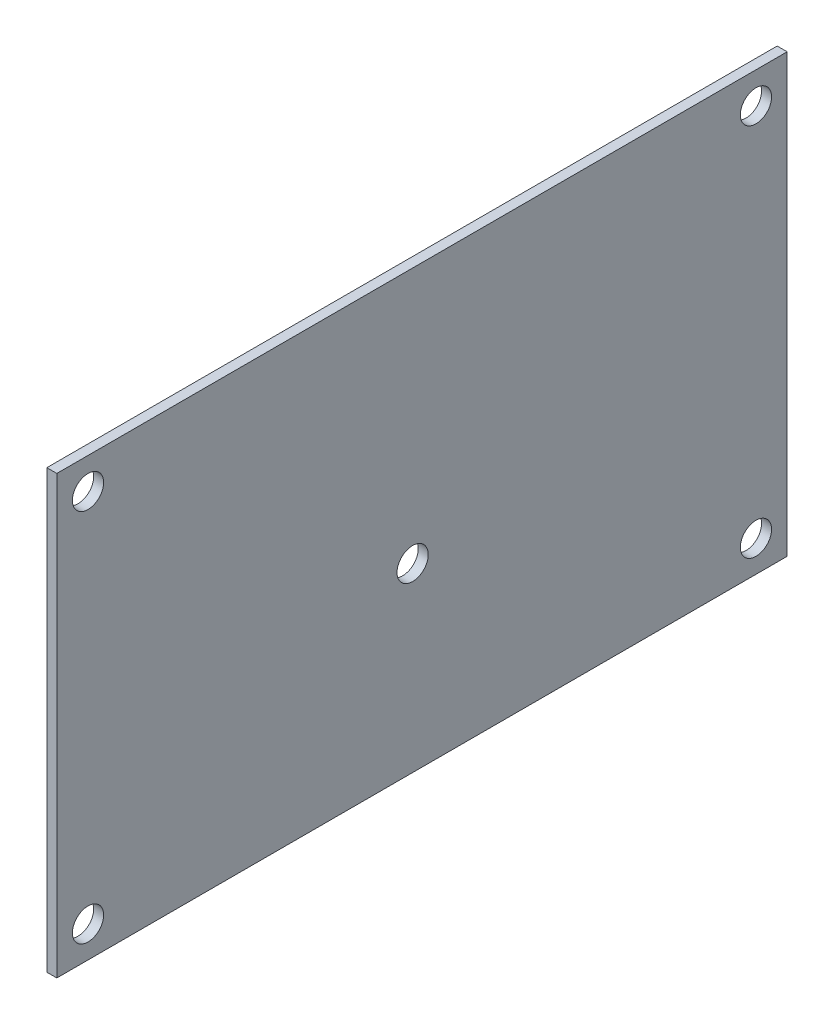
SolidWorks part; units mm, degrees
ref_plane "Front Plane" through (0, 0, 0) normal (0, 0, 1) x (1, 0, 0)
ref_plane "Top Plane" through (0, 0, 0) normal (0, 1, 0) x (1, 0, 0)
ref_plane "Right Plane" through (0, 0, 0) normal (1, 0, 0) x (0, 0, -1)
sketch "Sketch1" plane through (0, 0, 0) normal (1, 0, 0) x (0, 0, -1)
  line L1 (0, 0) -> (117, 0)
  line L2 (0, 0) -> (0, 70)
  line L3 (0, 70) -> (117, 70)
  line L4 (117, 0) -> (117, 70)
  dimension "D1" = 117
  dimension "D2" = 70
extrude "Boss-Extrude1" add sketch "Sketch1" along normal blind 1.6
sketch "Sketch2" plane through (1.6, 0, 0) normal (1, 0, 0) x (0, 0, -1)
  line L0 (117, 70) -> (0, 70) construction
  line L1 (0, 70) -> (0, 0) construction
  line L2 (0, 0) -> (117, 0) construction
  line L3 (117, 0) -> (117, 70) construction
  circle A0 centre (5, 65) radius 2.5
  circle A1 centre (5, 5) radius 2.5
  circle A2 centre (112, 5) radius 2.5
  circle A3 centre (112, 65) radius 2.5
  circle A4 centre (57, 29) radius 2.5
  dimension "D1" = 5
  dimension "D3" = 5
  dimension "D9" = 57
  dimension "D2" = 5
  dimension "D4" = 5
  dimension "D5" = 5
  dimension "D6" = 5
  dimension "D7" = 5
  dimension "D8" = 5
  dimension "D10" = 29
extrude "Cut-Extrude1" cut sketch "Sketch2" against normal through all
